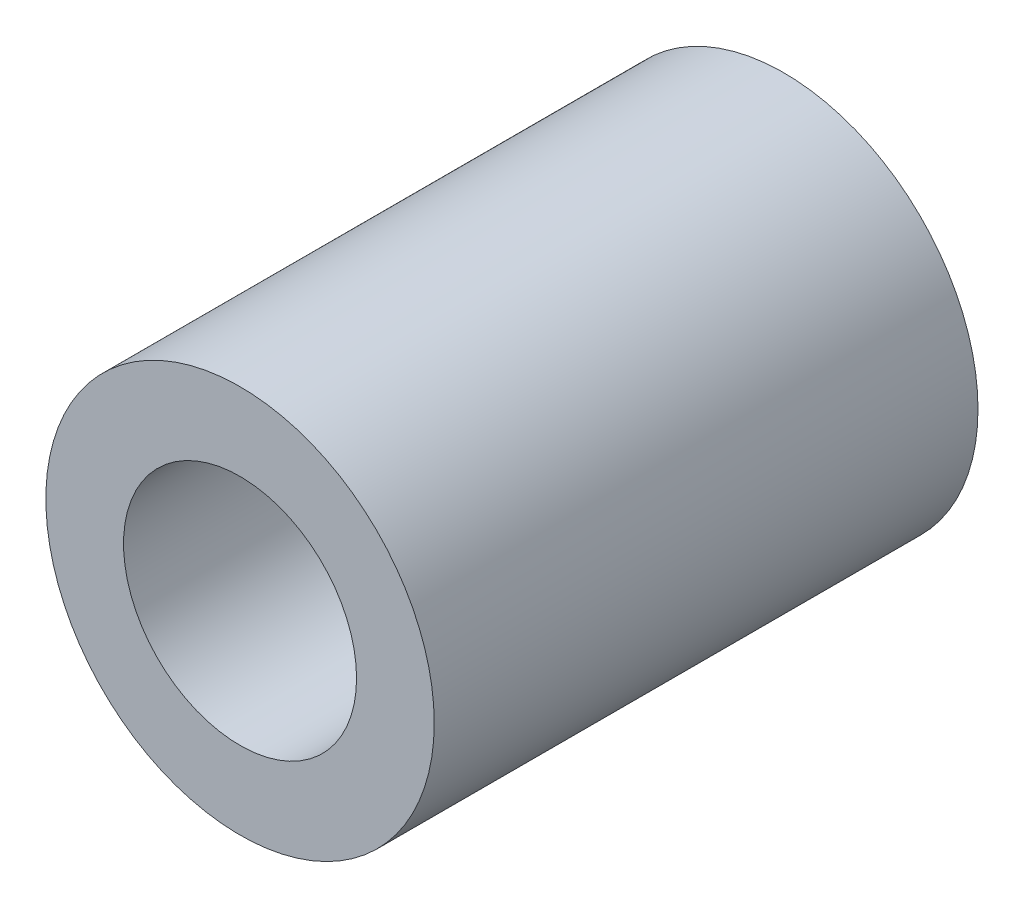
SolidWorks part; units mm, degrees
material "ﾎﾟﾘｵｷｼﾒﾁﾚﾝ(POM)ｱｾﾀｰﾙ共重合体"
ref_plane "Front Plane" through (0, 0, 0) normal (0, 0, 1) x (1, 0, 0)
ref_plane "Top Plane" through (0, 0, 0) normal (0, 1, 0) x (1, 0, 0)
ref_plane "Right Plane" through (0, 0, 0) normal (1, 0, 0) x (0, 0, -1)
sketch "Sketch2" plane through (0, 0, 0) normal (0, 0, 1) x (1, 0, 0)
  circle A0 centre (0, 0) radius 2.5
  circle A1 centre (0, 0) radius 1.5
  dimension "D1" = 3
  dimension "D2" = 5
  dimension "D3" = 5
extrude "Boss-Extrude1" add sketch "Sketch2" along normal blind 7
